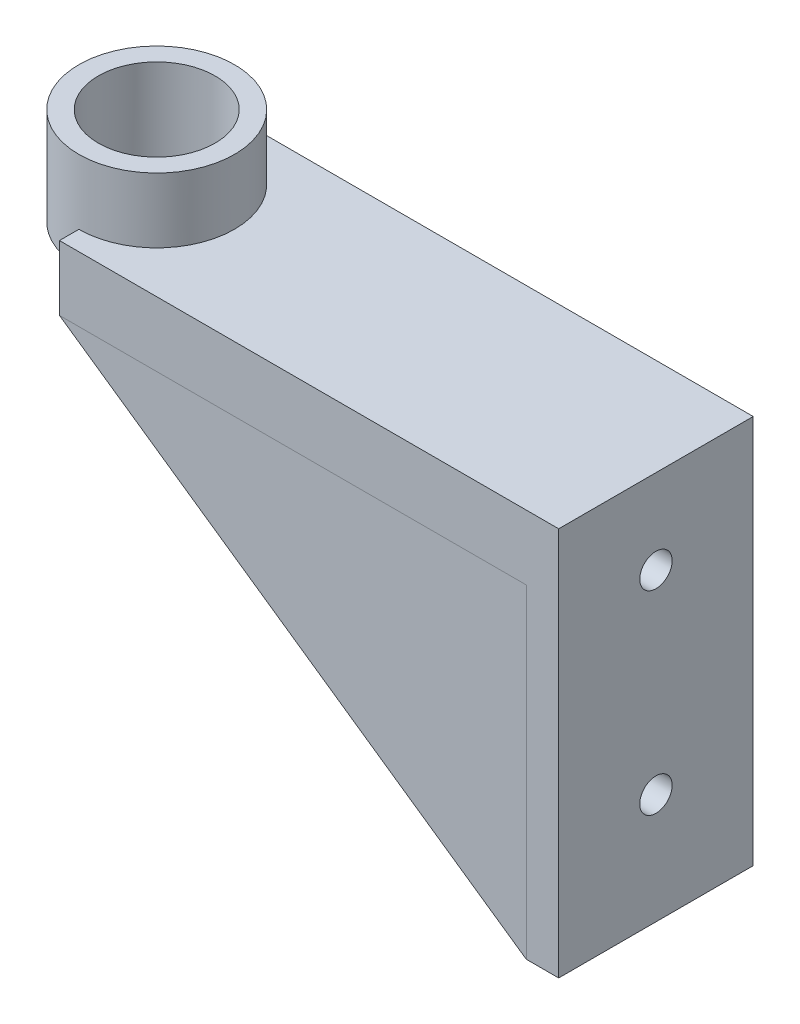
SolidWorks part; units mm, degrees
ref_plane "Front Plane" through (0, 0, 0) normal (0, 0, 1) x (1, 0, 0)
ref_plane "Top Plane" through (0, 0, 0) normal (0, 1, 0) x (1, 0, 0)
ref_plane "Right Plane" through (0, 0, 0) normal (1, 0, 0) x (0, 0, -1)
sketch "Sketch1" plane through (0, 0, 0) normal (0, 1, 0) x (1, 0, 0)
  circle A0 centre (0, 0) radius 9
  circle A1 centre (0, 0) radius 12
  dimension "D1" = 18
  dimension "D2" = 24
extrude "Boss-Extrude1" add sketch "Sketch1" along normal blind 15
sketch "Sketch2" plane through (0, 0, 0) normal (1, 0, 0) x (0, 0, -1)
  line L1 (-15, -5) -> (15, -5)
  line L2 (-15, -5) -> (-15, 5)
  line L3 (-15, 5) -> (15, 5)
  line L4 (15, -5) -> (15, 5)
  line L5 (-15, -5) -> (15, 5) construction
  line L6 (-15, 5) -> (15, -5) construction
  point P0 (0, 0)
  dimension "D1" = 10
  dimension "D2" = 30
extrude "Boss-Extrude2" add sketch "Sketch2" along normal blind 77
sketch "Sketch4" plane through (0, 5, 0) normal (0, 1, 0) x (1, 0, 0)
  line L0 (0, 9) -> (0, -9) construction
  line L1 (0, 9) -> (0, -9)
  arc A0 (0, -9) -> (0, 9) centre (0, 0) ccw construction
  arc A1 (0, -9) -> (0, 9) centre (0, 0) ccw
extrude "Cut-Extrude3" cut sketch "Sketch4" against normal blind 5
sketch "Sketch5" plane through (0, -5, 0) normal (0, -1, 0) x (1, 0, 0)
  line L0 (77, -15) -> (0, -15) construction
  line L1 (77, 15) -> (72, 15)
  line L2 (77, 15) -> (77, -15)
  line L3 (77, -15) -> (72, -15)
  line L4 (72, 15) -> (72, -15)
  dimension "D1" = 5
extrude "Boss-Extrude3" add sketch "Sketch5" along normal blind 50
sketch "Sketch6" plane through (72, 0, 0) normal (-1, 0, 0) x (0, 0, 1)
  line L0 (15, -5) -> (-15, -5) construction
  line L1 (-15, -55) -> (-15, -5) construction
  circle A0 centre (0, -8) radius 2.5
  circle A1 centre (0, -38) radius 2.5
  dimension "D1" = 5
  dimension "D2" = 5
  dimension "D3" = 3
  dimension "D4" = 30
  dimension "D5" = 15
  dimension "D6" = 15
extrude "Cut-Extrude4" cut sketch "Sketch6" against normal blind 5
sketch "Sketch7" plane through (0, 0, -15) normal (0, 0, -1) x (-1, 0, 0)
  line L0 (-72, -55) -> (0, -5)
  line L1 (0, -5) -> (-72, -5)
  line L2 (-72, -5) -> (-72, -55)
extrude "Boss-Extrude4" add sketch "Sketch7" against normal blind 5
sketch "Sketch8" plane through (0, 0, 15) normal (0, 0, 1) x (1, 0, 0)
  line L0 (0, -5) -> (72, -5)
  line L1 (72, -5) -> (72, -55)
  line L2 (72, -55) -> (0, -5)
extrude "Boss-Extrude5" add sketch "Sketch8" against normal blind 5 separate body
